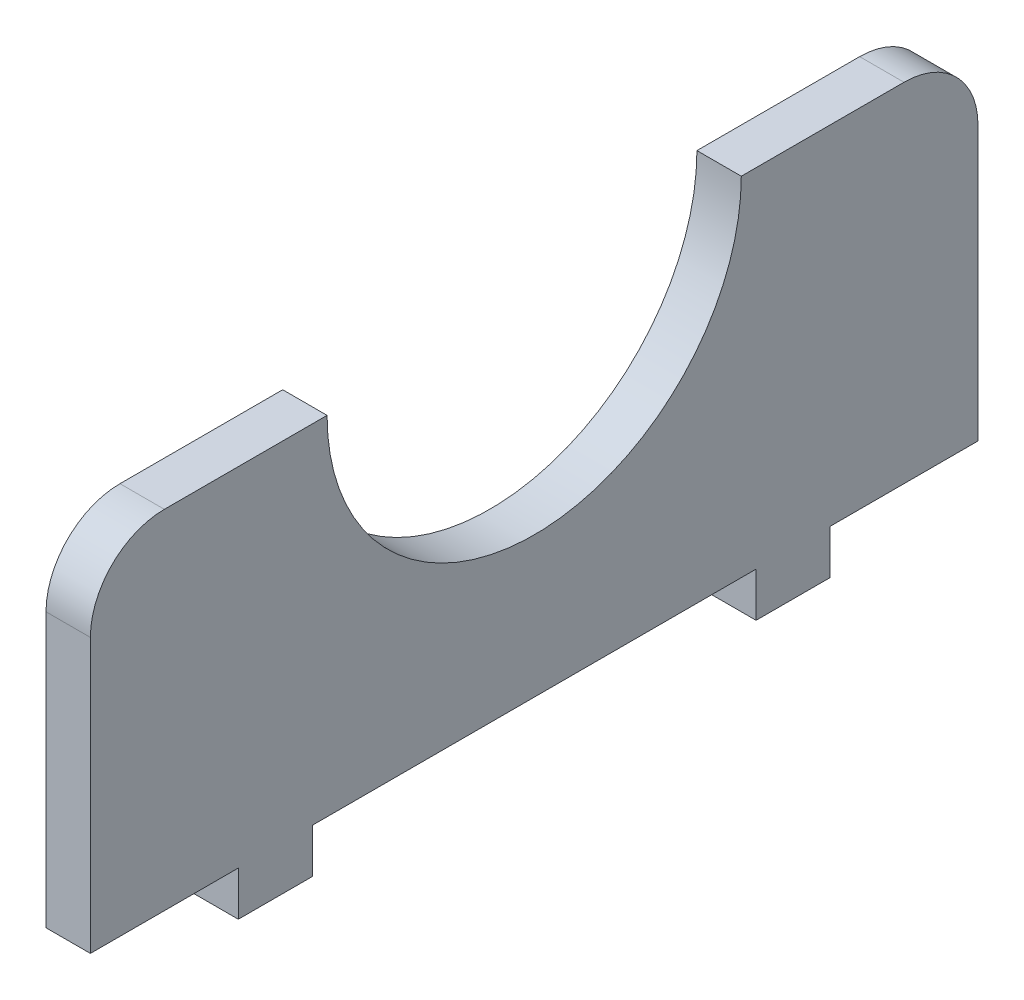
SolidWorks part; units mm, degrees
ref_plane "Front Plane" through (0, 0, 0) normal (0, 0, 1) x (1, 0, 0)
ref_plane "Top Plane" through (0, 0, 0) normal (0, 1, 0) x (1, 0, 0)
ref_plane "Right Plane" through (0, 0, 0) normal (1, 0, 0) x (0, 0, -1)
ref_plane "Plane1" through (0, -2, 0) normal (0, 1, 0) x (1, 0, 0)
sketch "Sketch1" plane through (0, 0, 0) normal (1, 0, 0) x (0, 0, -1)
  line L0 (-14, 11.75) -> (-30, 11.75)
  line L1 (30, -11.75) -> (-30, -11.75)
  line L2 (30, -11.75) -> (30, 11.75)
  line L3 (30, 11.75) -> (14, 11.75)
  line L4 (-30, -11.75) -> (-30, 11.75)
  line L5 (30, -11.75) -> (-30, 11.75) construction
  line L6 (30, 11.75) -> (-30, -11.75) construction
  arc A0 (-14, 11.75) -> (14, 11.75) centre (0, 11.75) ccw
  point P0 (0, 0)
  dimension "D4" = 28
  dimension "D2" = 60
  dimension "D3" = 23.5
extrude "Boss-Extrude1" add sketch "Sketch1" along normal blind 3
fillet "Fillet1" radius 5 2 edges at (1.5, 11.75, -30) (1.5, 11.75, 30)
sketch "Sketch3" plane through (0, -11.75, 0) normal (0, -1, 0) x (1, 0, 0)
  line L0 (3, 30) -> (3, -30) construction
  line L1 (3, 20) -> (0, 20)
  line L2 (3, 20) -> (3, 15)
  line L3 (3, 15) -> (0, 15)
  line L4 (0, 20) -> (0, 15)
  line L5 (0, 30) -> (0, -30) construction
  line L6 (3, 30) -> (0, 30) construction
  dimension "D1" = 10
  dimension "D2" = 5
extrude "Boss-Extrude2" add sketch "Sketch3" along normal blind 3
mirror "Mirror3" about plane through (0, 0, 0) normal (0, 0, 1) of "Boss-Extrude2"
